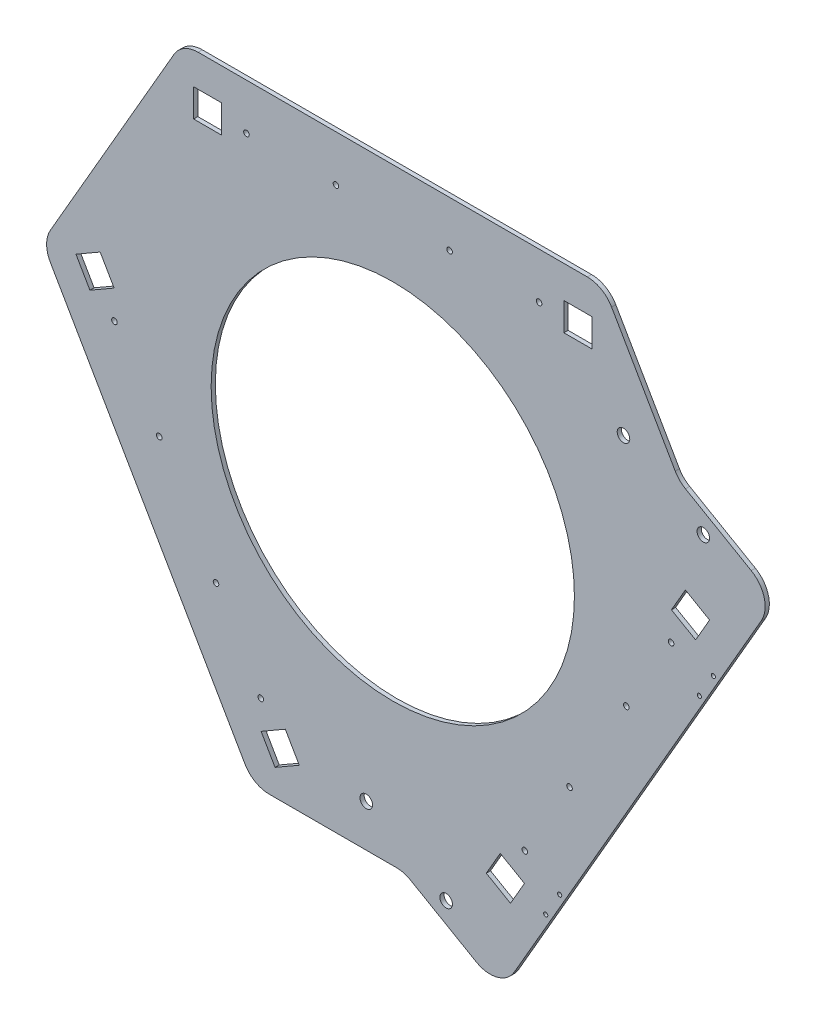
SolidWorks part; units mm, degrees
ref_plane "前视基准面" through (0, 0, 0) normal (0, 0, 1) x (1, 0, 0)
ref_plane "上视基准面" through (0, 0, 0) normal (0, 1, 0) x (1, 0, 0)
ref_plane "右视基准面" through (0, 0, 0) normal (1, 0, 0) x (0, 0, -1)
other "Configuration Table"
sketch "草图1" plane through (0, 0, 0) normal (0, 0, 1) x (1, 0, 0)
  line L0 (150.8286, 202.551) -> (-150.8286, 202.551)
  line L1 (-150.8286, 202.551) -> (-250.8286, 29.3459)
  line L2 (-250.8286, 29.3459) -> (-100, -231.8969)
  line L3 (-100, -231.8969) -> (100, -231.8969)
  line L4 (100, -231.8969) -> (250.8286, 29.3459)
  line L6 (-200.8286, 115.9485) -> (175.4143, -101.2755) construction
  line L7 (0, 202.551) -> (0, -231.8969) construction
  line L8 (-175.4143, -101.2755) -> (200.8262, 115.9471)
  line L9 (150.8286, 202.551) -> (250.8286, 29.3459)
  line L10 (-122.5, 179.551) -> (122.5, 179.551) construction
  line L11 (-122.5, 179.551) -> (122.5, 179.551)
  line L12 (-122.5, 159.551) -> (122.5, 159.551) construction
  line L13 (-122.5, 159.551) -> (122.5, 159.551)
  line L14 (-122.5, 179.551) -> (-122.5, 159.551)
  line L15 (-122.5, 169.551) -> (122.5, 169.551)
  line L16 (122.5, 159.551) -> (122.5, 179.551) construction
  line L17 (-122.5, 159.551) -> (-122.5, 179.551) construction
  circle A0 centre (0, 0) radius 130
  circle A2 centre (-104.7118, 169.551) radius 2
  circle A3 centre (-40.6669, 169.551) radius 2
  circle A4 centre (40.6669, 169.551) radius 2
  circle A5 centre (104.7118, 169.551) radius 2
  circle A6 centre (94.4796, -175.4585) radius 2
  circle A7 centre (126.502, -119.9941) radius 2
  circle A8 centre (167.1689, -49.5569) radius 2
  circle A9 centre (199.1913, 5.9076) radius 2
  circle A10 centre (-199.1913, 5.9076) radius 2
  circle A11 centre (-167.1689, -49.5569) radius 2
  circle A12 centre (-126.502, -119.9941) radius 2
  circle A13 centre (-94.4796, -175.4585) radius 2
  circle A18 centre (109.4502, -207.5287) radius 1.5
  circle A19 centre (119.4502, -190.2082) radius 1.5
  circle A20 centre (219.4502, -17.0031) radius 1.5
  circle A21 centre (229.4502, 0.3174) radius 1.5
  point P7 (0, 0)
  point P51 (0, 0)
  point P56 (0, 0)
  point P70 (-122.2962, -44.0868)
  dimension "D7" = 3
  dimension "D3" = 260
  dimension "D1" = 120
  dimension "D2" = 120
  dimension "D4" = 4
  dimension "D5" = 4
  dimension "D6" = 200
extrude "凸台-拉伸1" add sketch "草图1" along normal blind 3
sketch "草图8" plane through (0, 0, 3) normal (0, 0, 1) x (1, 0, 0)
  line L0 (-142.5, 179.551) -> (-142.5, 159.551)
  line L1 (-142.5, 179.551) -> (-122.5, 179.551)
  line L2 (-142.5, 159.551) -> (-122.5, 159.551)
  line L3 (-122.5, 179.551) -> (-122.5, 159.551)
  line L4 (-175.4143, -101.2755) -> (0, 0)
  line L5 (-209.4252, 43.6331) -> (-226.7457, 33.6331)
  line L6 (-209.4252, 43.6331) -> (-199.4252, 26.3126)
  line L7 (-226.7457, 33.6331) -> (-216.7457, 16.3126)
  line L8 (-199.4252, 26.3126) -> (-216.7457, 16.3126)
  line L9 (-84.2457, -213.1841) -> (-66.9252, -203.1841)
  line L10 (-84.2457, -213.1841) -> (-94.2457, -195.8636)
  line L11 (-66.9252, -203.1841) -> (-76.9252, -185.8636)
  line L12 (-94.2457, -195.8636) -> (-76.9252, -185.8636)
  line L13 (66.9252, -203.1841) -> (84.2457, -213.1841)
  line L14 (66.9252, -203.1841) -> (76.9252, -185.8636)
  line L15 (84.2457, -213.1841) -> (94.2457, -195.8636)
  line L16 (76.9252, -185.8636) -> (94.2457, -195.8636)
  line L17 (209.4252, 43.6331) -> (199.4252, 26.3126)
  line L18 (209.4252, 43.6331) -> (226.7457, 33.6331)
  line L19 (199.4252, 26.3126) -> (216.7457, 16.3126)
  line L20 (226.7457, 33.6331) -> (216.7457, 16.3126)
  line L21 (142.5, 179.551) -> (142.5, 159.551)
  line L22 (142.5, 179.551) -> (122.5, 179.551)
  line L23 (142.5, 159.551) -> (122.5, 159.551)
  line L24 (122.5, 179.551) -> (122.5, 159.551)
  line L25 (0, 0) -> (175.4143, -101.2755)
  line L26 (0, 202.551) -> (0, 0)
  line L28 (150.8286, 202.551) -> (-150.8286, 202.551) construction
  line L29 (100, -231.8969) -> (250.8286, 29.3459) construction
  line L31 (-250.8286, 29.3459) -> (-100, -231.8969) construction
  dimension "D1" = 20
  dimension "D2" = 20
  dimension "D3" = 20
  dimension "D4" = 20
  dimension "D5" = 20
  dimension "D6" = 20
  dimension "D7" = 20
  dimension "D8" = 20
  dimension "D9" = 20
  dimension "D10" = 20
  dimension "D11" = 23
  dimension "D12" = 245
  dimension "D13" = 245
  dimension "D14" = 23
  dimension "D15" = 245
  dimension "D16" = 23
  dimension "D17" = 122.5
  dimension "D18" = 122.5
  dimension "D19" = 122.5
  dimension "D21" = 20
  dimension "D22" = 20
extrude "切除-拉伸4" cut sketch "草图8" against normal through all contours L0 L1 L3 L2 | L5 L6 L8 L7 | L21 L22 L24 L23 | L17 L18 L20 L19 | L9 L10 L12 L11 | L13 L14 L16 L15
fillet "圆角2" radius 20 6 edges at (100, -231.8969, 1.5) (-100, -231.8969, 1.5) (150.8286, 202.551, 1.5) (250.8286, 29.3459, 1.5) (-250.8286, 29.3459, 1.5) (-150.8286, 202.551, 1.5)
sketch "草图9" plane through (0, 0, 3) normal (0, 0, 1) x (1, 0, 0)
  line L0 (8.007, -231.8969) -> (77.0018, -271.731)
  line L1 (-88.453, -231.8969) -> (88.453, -231.8969) construction
  line L2 (77.0018, -271.731) -> (117.6129, -201.3904)
  line L3 (105.7735, -221.8969) -> (245.0551, 19.3459) construction
  line L4 (175.4143, -101.2755) -> (117.6129, -67.9038)
  line L5 (273.8269, 69.18) -> (233.2157, -1.1605)
  line L6 (204.8321, 109.0142) -> (273.8269, 69.18)
  line L11 (-88.453, -231.8969) -> (88.453, -231.8969)
  line L12 (105.7735, -221.8969) -> (245.0551, 19.3459)
  line L13 (245.0551, 39.3459) -> (156.6021, 192.551)
  line L14 (139.2816, 202.551) -> (-139.2816, 202.551)
  line L15 (-156.6021, 192.551) -> (-245.0551, 39.3459)
  line L16 (-245.0551, 19.3459) -> (-105.7735, -221.8969)
  line L17 (-88.453, -231.8969) -> (88.453, -231.8969)
  line L18 (105.7735, -221.8969) -> (245.0551, 19.3459)
  line L19 (245.0551, 39.3459) -> (156.6021, 192.551)
  line L20 (139.2816, 202.551) -> (-139.2816, 202.551)
  line L21 (-156.6021, 192.551) -> (-245.0551, 39.3459)
  line L22 (-245.0551, 19.3459) -> (-105.7735, -221.8969)
  arc A6 (88.453, -231.8969) -> (105.7735, -221.8969) centre (88.453, -211.8969) ccw
  arc A7 (245.0551, 19.3459) -> (245.0551, 39.3459) centre (227.7346, 29.3459) ccw
  arc A8 (156.6021, 192.551) -> (139.2816, 202.551) centre (139.2816, 182.551) ccw
  arc A9 (-139.2816, 202.551) -> (-156.6021, 192.551) centre (-139.2816, 182.551) ccw
  arc A10 (-245.0551, 39.3459) -> (-245.0551, 19.3459) centre (-227.7346, 29.3459) ccw
  arc A11 (-105.7735, -221.8969) -> (-88.453, -231.8969) centre (-88.453, -211.8969) ccw
  arc A12 (88.453, -231.8969) -> (105.7735, -221.8969) centre (88.453, -211.8969) ccw
  arc A13 (245.0551, 19.3459) -> (245.0551, 39.3459) centre (227.7346, 29.3459) ccw
  arc A14 (156.6021, 192.551) -> (139.2816, 202.551) centre (139.2816, 182.551) ccw
  arc A15 (-139.2816, 202.551) -> (-156.6021, 192.551) centre (-139.2816, 182.551) ccw
  arc A16 (-245.0551, 39.3459) -> (-245.0551, 19.3459) centre (-227.7346, 29.3459) ccw
  arc A17 (-105.7735, -221.8969) -> (-88.453, -231.8969) centre (-88.453, -211.8969) ccw
  dimension "D1" = 0
extrude "凸台-拉伸2" add sketch "草图9" against normal blind 3
fillet "圆角3" radius 20 4 edges at (273.8269, 69.18, 1.5) (204.8321, 109.0142, 1.5) (77.0018, -271.731, 1.5) (8.007, -231.8969, 1.5)
sketch "草图10" plane through (0, 0, 3) normal (0, 0, 1) x (1, 0, 0)
  line L0 (175.4143, -101.2755) -> (142.6501, -82.3591)
  line L1 (87.0018, -254.4105) -> (263.8269, 51.8595) construction
  circle A0 centre (-18.9734, -201.6056) radius 4.5
  circle A1 centre (38.1827, -234.6047) radius 4.5
  circle A2 centre (222.2649, 84.2352) radius 4.5
  circle A3 centre (165.1088, 117.2342) radius 4.5
  dimension "D1" = 9
  dimension "D2" = 9
extrude "切除-拉伸5" cut sketch "草图10" against normal blind 3 contours A0 | A1 | A3 | A2
